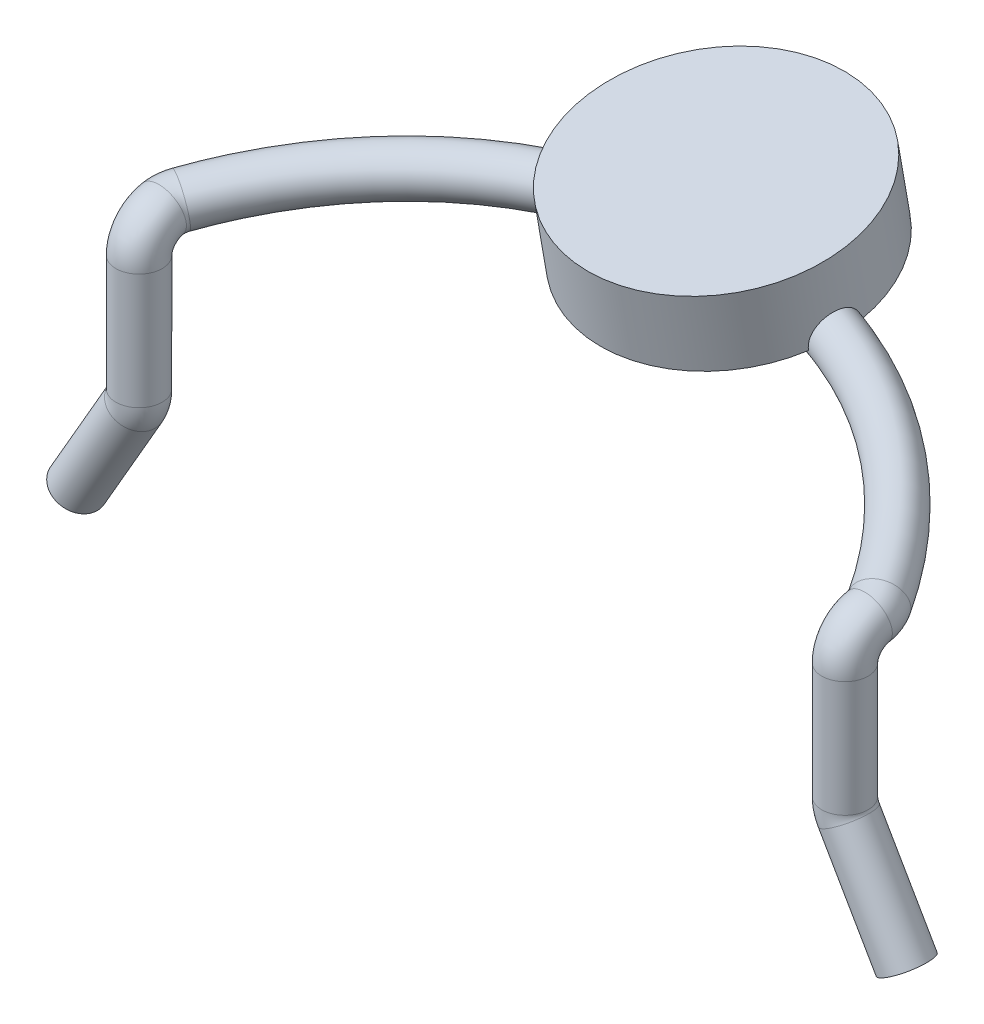
SolidWorks part; units mm, degrees
material "3.0517 (EN-AW 3003)"
ref_plane "Front Plane" through (0, 0, 0) normal (0, 0, 1) x (1, 0, 0)
ref_plane "Top Plane" through (0, 0, 0) normal (0, 1, 0) x (1, 0, 0)
ref_plane "Right Plane" through (0, 0, 0) normal (1, 0, 0) x (0, 0, -1)
sketch "Sketch1" plane through (0, 0, 0) normal (0, 1, 0) x (1, 0, 0)
  line L0 (-6.5, 0) -> (6.5, 0) construction
  circle A0 centre (-6.1, 0) radius 0.4
  circle A1 centre (6.1, 0) radius 0.4
  dimension "D1" = 0.8
  dimension "D2" = 13
extrude "Boss-Extrude1" add sketch "Sketch1" against normal blind 2
sketch "Sketch2" plane through (0, 0, 0) normal (0, 1, 0) x (1, 0, 0)
  line L0 (-6.5, 0.5) -> (6.5, 0.5) construction
  line L1 (0, 0.5) -> (0, 0) construction
  circle A0 centre (6.1, 0) radius 0.4 construction
  circle A1 centre (-6.1, 0) radius 0.4 construction
  circle A2 centre (6.1, 0) radius 0.4
  circle A3 centre (-6.1, 0) radius 0.4
  dimension "D1" = 13
  dimension "D2" = 0.5
revolve "Revolve4" add sketch "Sketch2" angle 80 about L0
sketch "Sketch3" plane through (0, 0.0855, -0.4849) normal (0, 0.1736, -0.9848) x (-1, 0, 0)
  line L0 (-6.1, 0.4132) -> (-5.6, 0.4132) construction
  line L1 (-5.6, 0.9106) -> (-5.6, -0.0842) construction
  circle A1 centre (-6.1, 0.4132) radius 0.4
  circle A2 centre (-6.1, 0.4132) radius 0.4
  dimension "D2" = 0.5
  dimension "D1" = 0
revolve "Revolve5" add sketch "Sketch3" angle 30 about L1
sketch "Sketch4" plane through (0, 0.0855, -0.4849) normal (0, 0.1736, -0.9848) x (-1, 0, 0)
  line L0 (6.1, 0.4132) -> (5.6, 0.4132) construction
  line L1 (5.6, 0.9666) -> (5.6, -0.1402) construction
  circle A1 centre (6.1, 0.4132) radius 0.4
  circle A2 centre (6.1, 0.4132) radius 0.4
  dimension "D2" = 0.5
  dimension "D1" = 0
revolve "Revolve6" add sketch "Sketch4" angle 30 about L1
ref_point "Point1"
ref_point "Point2"
ref_plane "Plane1" through (0, 0.4069, 0.0717) normal (0, 0.9848, 0.1736) x (1, 0, 0)
sketch "Sketch5" plane through (0, 0.4069, 0.0717) normal (0, 0.9848, 0.1736) x (1, 0, 0)
  line L0 (-5.6866, 0.5424) -> (-6.3794, 0.9424) construction
  line L1 (-5.6866, 0.5424) -> (-6.3794, 0.9424) construction
  line L2 (-6.033, 0.7424) -> (0, 11.1919) construction
  line L3 (6.3794, 0.9424) -> (5.6866, 0.5424) construction
  line L4 (6.3794, 0.9424) -> (5.6866, 0.5424) construction
  line L5 (6.033, 0.7424) -> (0, 11.1919) construction
  arc A0 (-6.033, 0.7424) -> (6.033, 0.7424) centre (0, -2.7408) cw
sketch "Sketch11" plane through (-1.1868, -0.3569, 2.0243) normal (0.5, 0.1504, -0.8529) x (-0.8403, -0.154, -0.5198)
  circle A1 centre (5.3297, 1.7549) radius 0.4
  circle A2 centre (5.3297, 1.7549) radius 0.4
  dimension "D1" = 0
sweep "Sweep1" add profiles "Sketch11" path "Sketch5"
sketch "Sketch12" plane through (0, 0.4069, 0.0717) normal (0, 0.9848, 0.1736) x (1, 0, 0)
  arc A0 (6.033, 0.7424) -> (-6.033, 0.7424) centre (0, -2.7408) ccw construction
  arc A1 (6.033, 0.7424) -> (-6.033, 0.7424) centre (0, -2.7408) ccw construction
  circle A2 centre (0, 4.2256) radius 2.25
  dimension "D1" = 4.5
extrude "Boss-Extrude2" add sketch "Sketch12" along normal blind 1.25
sketch "Sketch13" plane through (0, -2, 0) normal (0, -1, 0) x (1, 0, 0)
  line L0 (6.1, 0) -> (6.6, 0) construction
  line L1 (6.6, -0.2918) -> (6.6, 0.2918) construction
  circle A1 centre (6.1, 0) radius 0.4
  circle A2 centre (6.1, 0) radius 0.4
  dimension "D2" = 0.5
  dimension "D1" = 0
revolve "Revolve7" add sketch "Sketch13" angle 30 about L1
sketch "Sketch14" plane through (2.516, -4.3579, 0) normal (0.5, -0.866, 0) x (0.866, 0.5, 0)
  circle A1 centre (4.2158, 0) radius 0.4
  circle A2 centre (4.2158, 0) radius 0.4
  dimension "D1" = 0
extrude "Boss-Extrude3" add sketch "Sketch14" along normal blind 2
mirror "Mirror1" about plane through (0, 0, 0) normal (1, 0, 0) of "Boss-Extrude3", "Revolve7"
